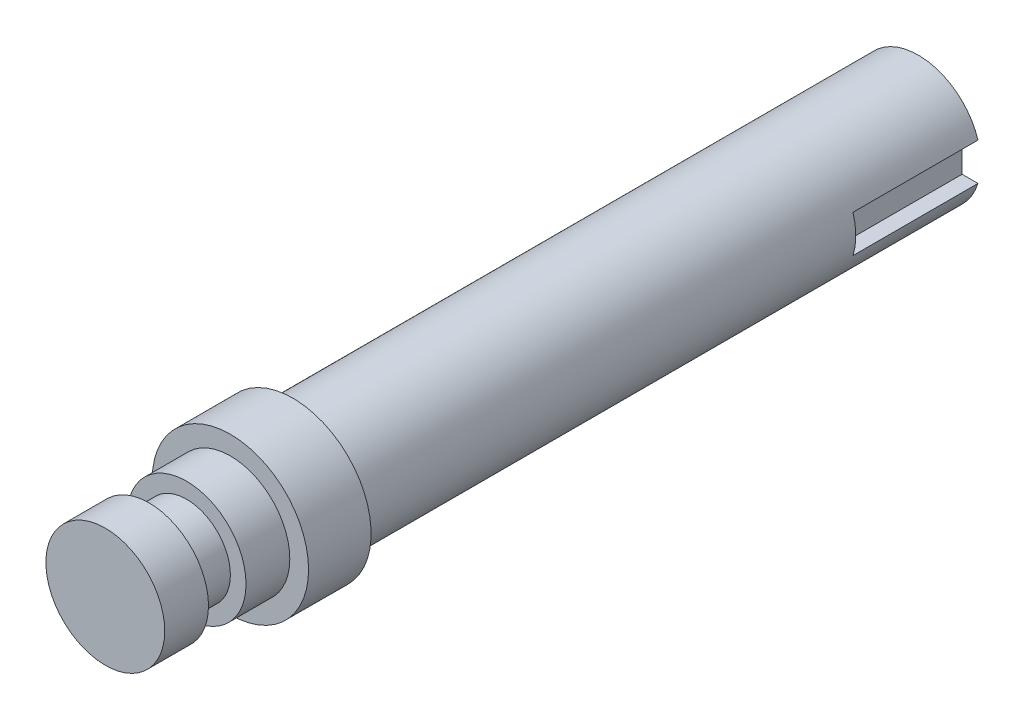
SolidWorks part; units mm, degrees
ref_plane "Ön Düzlem" through (0, 0, 0) normal (0, 0, 1) x (1, 0, 0)
ref_plane "Üst Düzlem" through (0, 0, 0) normal (0, 1, 0) x (1, 0, 0)
ref_plane "Sağ Düzlem" through (0, 0, 0) normal (1, 0, 0) x (0, 0, -1)
sketch "Çizim1" plane through (0, 0, 0) normal (0, 0, 1) x (1, 0, 0)
  circle A0 centre (0, 0) radius 12.5
  dimension "D1" = 25
extrude "Yükseklik-Ekstrüzyon1" add sketch "Çizim1" along normal mid plane 130
sketch "Çizim2" plane through (0, 0, -65) normal (0, 0, -1) x (-1, 0, 0)
  circle A0 centre (0, 0) radius 10
  circle A1 centre (0, 0) radius 12.5 construction
  circle A2 centre (0, 0) radius 12.5
  dimension "D1" = 20
extrude "Kes-Ekstrüzyon1" cut sketch "Çizim2" against normal blind 100
ref_plane "Düzlem1" through (10, 0, 0) normal (1, 0, 0) x (0, 0, -1)
sketch "Çizim3" plane through (10, 0, 0) normal (1, 0, 0) x (0, 0, -1)
  line L0 (65, 0) -> (32.3022, 0) construction
  line L1 (65, -10) -> (65, 10) construction
  line L2 (65, 3) -> (45, 3)
  line L3 (45, 3) -> (45, -3)
  line L5 (45, -3) -> (65, -3)
  line L6 (65, 3) -> (65, -3)
  dimension "D1" = 3
  dimension "D2" = 3
  dimension "D3" = 20
extrude "Kes-Ekstrüzyon2" cut sketch "Çizim3" against normal blind 3
sketch "Çizim4" plane through (0, 0, 65) normal (0, 0, 1) x (1, 0, 0)
  circle A0 centre (0, 0) radius 9.5
  circle A1 centre (0, 0) radius 12.5 construction
  circle A2 centre (0, 0) radius 12.5
  dimension "D1" = 19
extrude "Kes-Ekstrüzyon3" cut sketch "Çizim4" against normal blind 7
sketch "Çizim5" plane through (0, 0, 58) normal (0, 0, 1) x (1, 0, 0)
  circle A0 centre (0, 0) radius 7
  circle A1 centre (0, 0) radius 12.5 construction
  circle A2 centre (0, 0) radius 12.5
  dimension "D1" = 14
extrude "Kes-Ekstrüzyon4" cut sketch "Çizim5" against normal blind 6
sketch "Çizim6" plane through (0, 0, 52) normal (0, 0, 1) x (1, 0, 0)
  circle A0 centre (0, 0) radius 12.5 construction
  circle A1 centre (0, 0) radius 9.5 construction
  circle A2 centre (0, 0) radius 12.5
  circle A3 centre (0, 0) radius 9.5
extrude "Kes-Ekstrüzyon5" cut sketch "Çizim6" against normal blind 7
